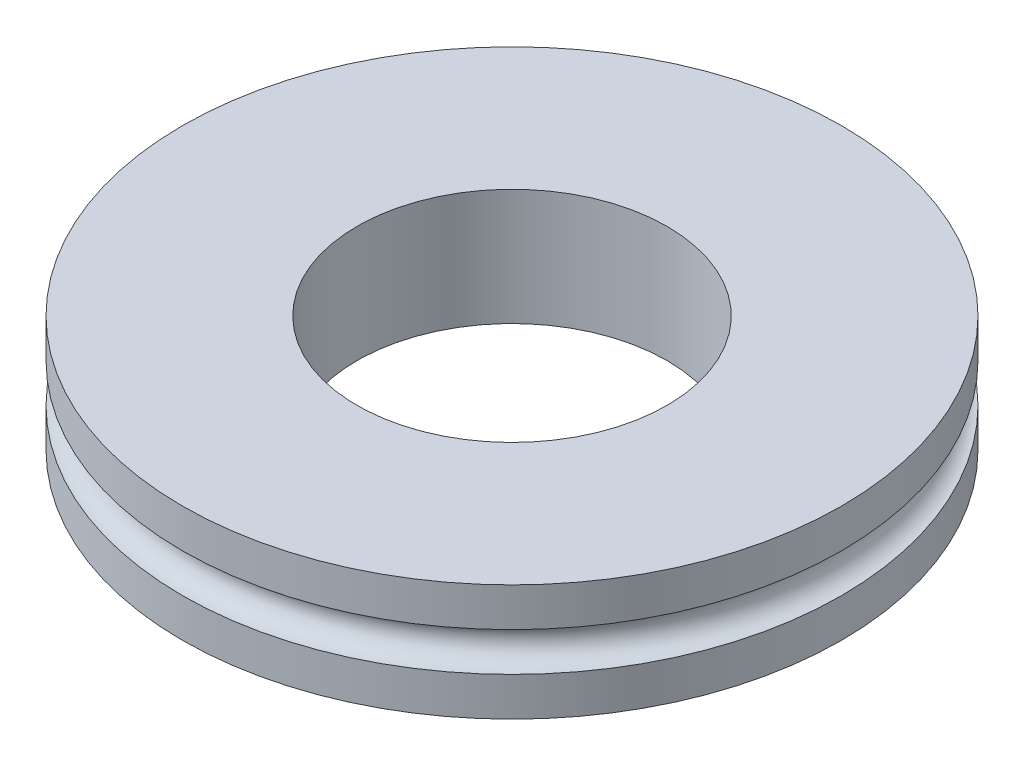
SolidWorks part; units mm, degrees
material "Custom Plastic"
ref_plane "Front Plane" through (0, 0, 0) normal (0, 0, 1) x (1, 0, 0)
ref_plane "Top Plane" through (0, 0, 0) normal (0, 1, 0) x (1, 0, 0)
ref_plane "Right Plane" through (0, 0, 0) normal (1, 0, 0) x (0, 0, -1)
sketch "Sketch1" plane through (0, 0, 0) normal (0, 0, 1) x (1, 0, 0)
  line L0 (0, -1.5) -> (0, 1.5) construction
  line L1 (0, 1.5) -> (8.5, 1.5) construction
  line L2 (8.5, 1.5) -> (8.5, -1.5) construction
  line L3 (8.5, -1.5) -> (0, -1.5) construction
  line L4 (4, 1.5) -> (4, -1.5)
  line L5 (4, 0.5) -> (8.5, 0.5) construction
  line L6 (4, -0.5) -> (8.5, -0.5) construction
  line L7 (8.5, -0.5) -> (8.5, -1.5)
  line L8 (8.5, -1.5) -> (4, -1.5)
  line L9 (4, 1.5) -> (8.5, 1.5)
  line L10 (8.5, 1.5) -> (8.5, 0.5)
  line L11 (4, 0) -> (8, 0) construction
  arc A0 (8.5, 0.5) -> (8.5, -0.5) centre (8.5, 0) ccw
  point P4 (0, 0)
  dimension "D2" = 8
  dimension "D3" = 1
  dimension "D1" = 4
  dimension "D4" = 1
revolve "Revolve1" add sketch "Sketch1" angle 360 about L0
